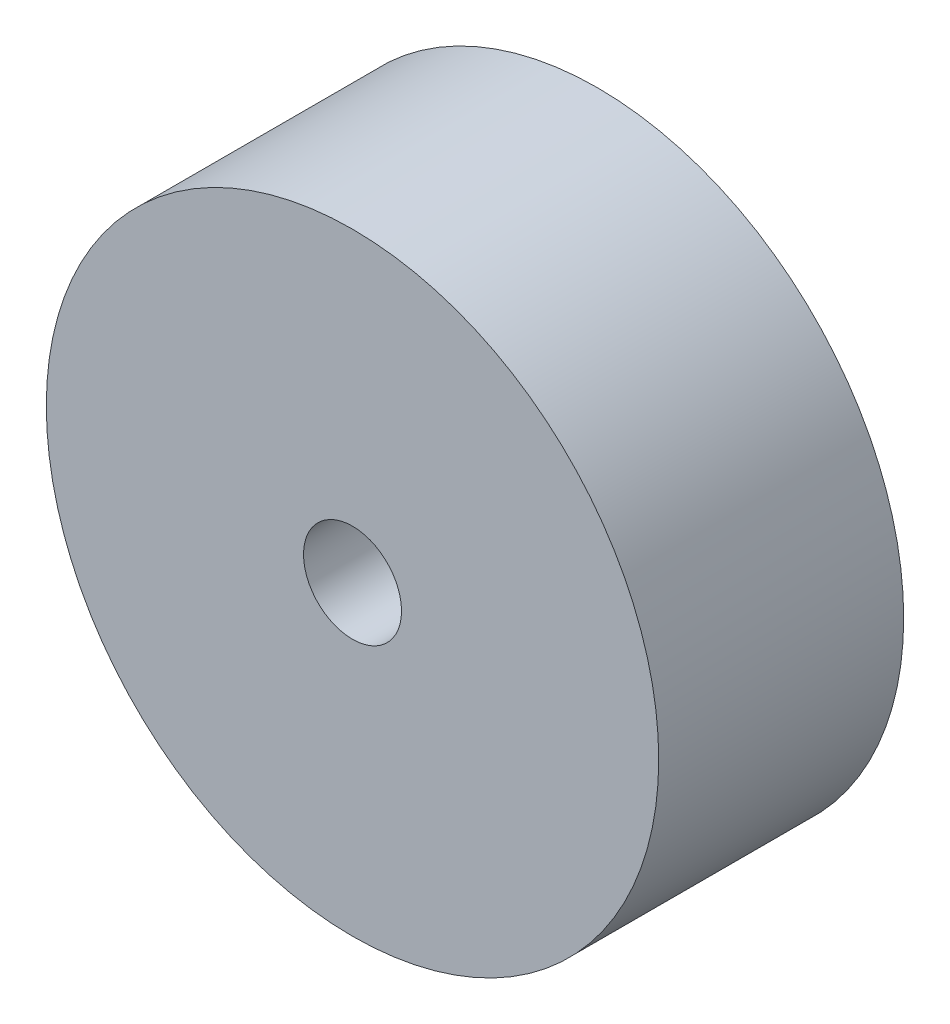
SolidWorks part; units mm, degrees
ref_plane "Front Plane" through (0, 0, 0) normal (0, 0, 1) x (1, 0, 0)
ref_plane "Top Plane" through (0, 0, 0) normal (0, 1, 0) x (1, 0, 0)
ref_plane "Right Plane" through (0, 0, 0) normal (1, 0, 0) x (0, 0, -1)
sketch "Croquis1" plane through (0, 0, 0) normal (0, 0, 1) x (1, 0, 0)
  circle A0 centre (0, 0) radius 0.625
  circle A1 centre (0, 0) radius 0.1
  dimension "D1" = 1.25
  dimension "D2" = 0.2
extrude "Saliente-Extruir1" add sketch "Croquis1" along normal blind 0.5
sketch "Croquis2" plane through (0, 0, 0) normal (0, 1, 0) x (1, 0, 0)
  line L0 (0, -0.125) -> (0, 0) construction
  line L1 (0, 0) -> (0.2795, 0) construction
  line L2 (0.625, 0) -> (-0.625, 0) construction
  line L3 (0, 0) -> (0, -0.125)
  line L4 (0, 0) -> (0.2795, 0)
  arc A0 (0, -0.125) -> (0.2795, 0) centre (0, 0.25) ccw
  dimension "D1" = 0.75
  dimension "D2" = 0.25
revolve "Cortar-Revolución3" cut sketch "Croquis2" angle 360 about L3
fillet "Redondeo1" radius 0.15 1 edges at (-0.1, 0, 0.1114)
